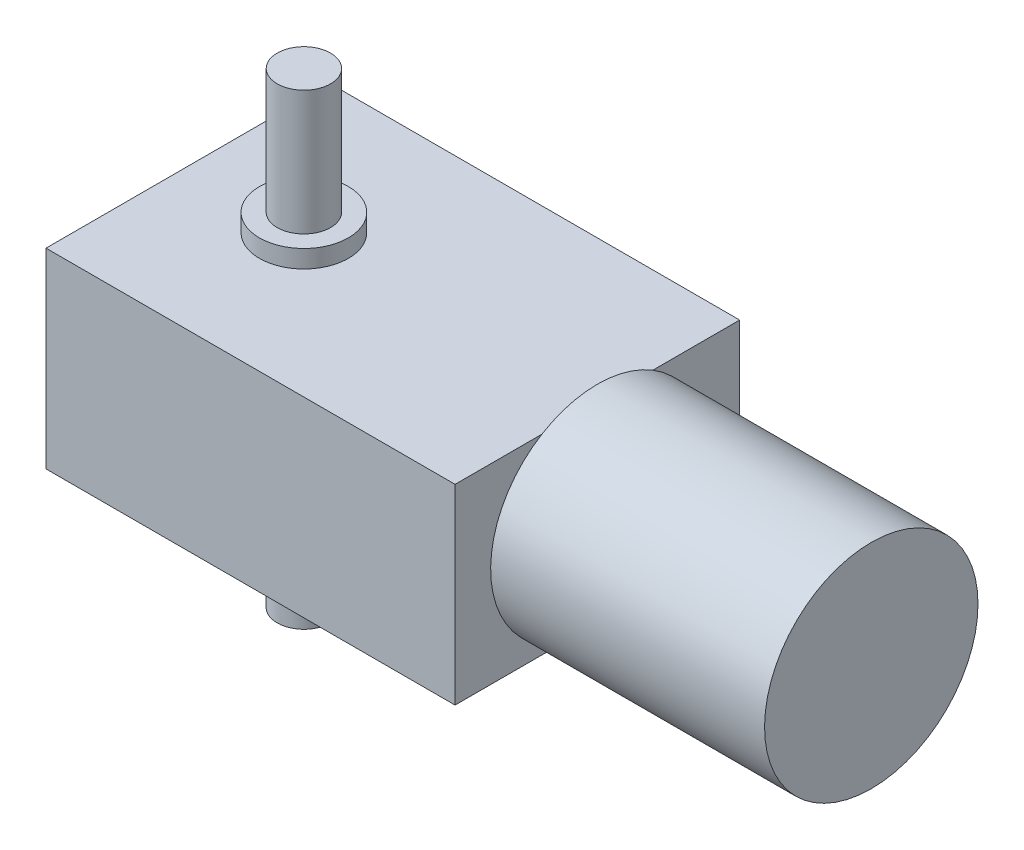
SolidWorks part; units mm, degrees
ref_plane "前视基准面" through (0, 0, 0) normal (0, 0, 1) x (1, 0, 0)
ref_plane "上视基准面" through (0, 0, 0) normal (0, 1, 0) x (1, 0, 0)
ref_plane "右视基准面" through (0, 0, 0) normal (1, 0, 0) x (0, 0, -1)
sketch "草图2" plane through (0, 0, 0) normal (0, 0, 1) x (1, 0, 0)
  line L0 (-20.3529, 27.756) -> (-20.3529, 6.256)
  line L1 (-20.3529, 6.256) -> (25.6471, 6.256)
  line L2 (25.6471, 6.256) -> (25.6471, 27.756)
  line L3 (25.6471, 27.756) -> (-20.3529, 27.756)
extrude "凸台-拉伸1" add sketch "草图2" along normal blind 32
sketch "草图3" plane through (0, 27.756, 0) normal (0, 1, 0) x (1, 0, 0)
  line L0 (-20.3529, -16) -> (-7.3529, -16) construction
  line L1 (-20.3529, -32) -> (-20.3529, 0) construction
  circle A0 centre (-7.3529, -16) radius 5
extrude "凸台-拉伸2" add sketch "草图3" along normal blind 2
sketch "草图4" plane through (0, 29.756, 0) normal (0, 1, 0) x (1, 0, 0)
  circle A0 centre (-7.3529, -16) radius 3
extrude "凸台-拉伸3" add sketch "草图4" along normal blind 14
ref_plane "基准面1" through (0, 17.506, 0) normal (0, 1, 0) x (1, 0, 0)
mirror "镜向1" about plane through (0, 17.506, 0) normal (0, 1, 0) of "凸台-拉伸3", "凸台-拉伸2"
sketch "草图5" plane through (25.6471, 0, 0) normal (1, 0, 0) x (0, 0, -1)
  line L0 (17.6, 17.506) -> (-17.6, 17.506) construction
  circle A0 centre (-16, 17.506) radius 12
extrude "凸台-拉伸4" add sketch "草图5" along normal blind 30.8
